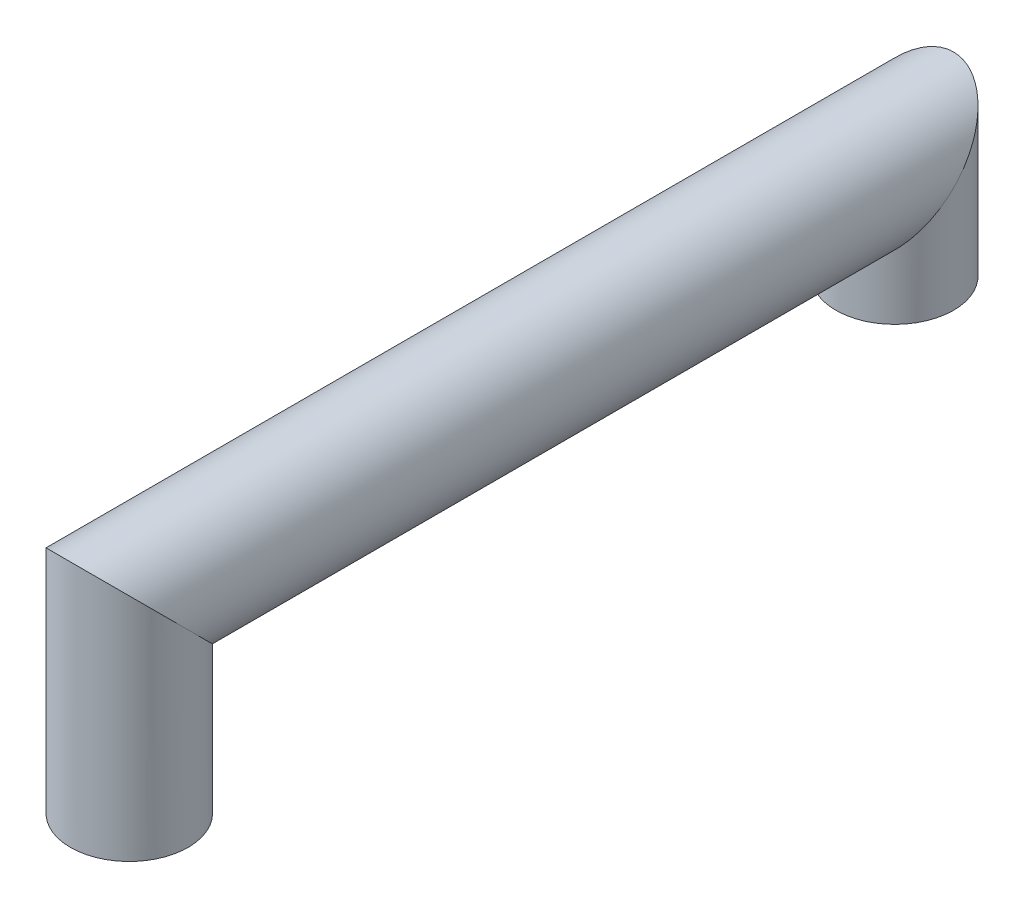
SolidWorks part; units mm, degrees
ref_plane "Front Plane" through (0, 0, 0) normal (0, 0, 1) x (1, 0, 0)
ref_plane "Top Plane" through (0, 0, 0) normal (0, 1, 0) x (1, 0, 0)
ref_plane "Right Plane" through (0, 0, 0) normal (1, 0, 0) x (0, 0, -1)
sketch "Sketch1" plane through (0, 0, 0) normal (0, 1, 0) x (1, 0, 0)
  line L0 (0, -5.5) -> (0, 5.5) construction
  circle A0 centre (0, 0) radius 5
  dimension "D1" = 10
sketch "Sketch2" plane through (0, 0, 0) normal (1, 0, 0) x (0, 0, -1)
  line L0 (0, 0) -> (0, 16)
  line L1 (5, 0) -> (-5, 0) construction
  line L2 (0, 16) -> (65, 16)
  line L3 (65, 16) -> (65, 7)
  dimension "D1" = 9
sweep "Sweep1" add profiles "Sketch1" path "Sketch2"
